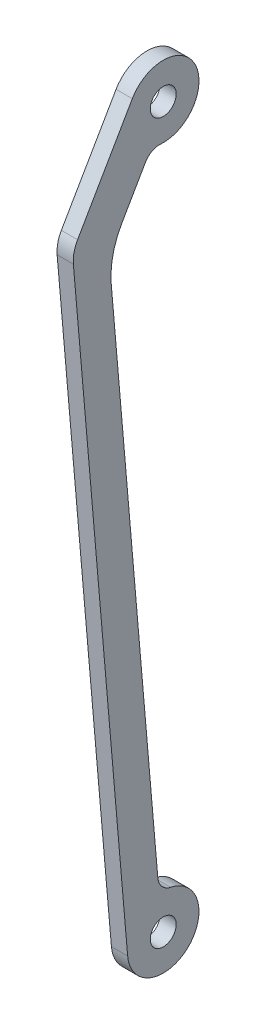
SolidWorks part; units mm, degrees
ref_plane "Front Plane" through (0, 0, 0) normal (0, 0, 1) x (1, 0, 0)
ref_plane "Top Plane" through (0, 0, 0) normal (0, 1, 0) x (1, 0, 0)
ref_plane "Right Plane" through (0, 0, 0) normal (1, 0, 0) x (0, 0, -1)
sketch "Sketch1" plane through (0, 0, 0) normal (0, 1, 0) x (1, 0, 0)
  line L1 (-5.5, -9.5263) -> (23.6733, -26.3695)
  line L2 (40.742, -16.0057) -> (206.1791, -1.6657)
  line L3 (26.0831, -12.7497) -> (13.4599, -5.4617)
  line L6 (29.5368, -27.6719) -> (222.3499, -10.9589)
  circle A0 centre (0, 0) radius 4
  arc A1 (10.9725, -0.778) -> (-5.5, -9.5263) centre (0, 0) ccw
  circle A2 centre (221.4, 0) radius 4
  arc A3 (222.3499, -10.9589) -> (210.6388, 2.2795) centre (221.4, 0) ccw
  arc A4 (10.9725, -0.778) -> (13.4599, -5.4617) centre (15.9599, -1.1316) ccw
  arc A5 (26.0831, -12.7497) -> (40.742, -16.0057) centre (38.5831, 8.9009) ccw
  arc A6 (206.1791, -1.6657) -> (210.6388, 2.2795) centre (205.7473, 3.3156) ccw
  arc A8 (23.6733, -26.3695) -> (29.5368, -27.6719) centre (28.6733, -17.7092) ccw
  dimension "D1" = 8
  dimension "D2" = 22
  dimension "D4" = 8
  dimension "D5" = 22
  dimension "D6" = 10
  dimension "D7" = 50
  dimension "D8" = 227.8499
  dimension "D9" = 193.5361
  dimension "D10" = 33.6864
  dimension "D13" = 10
  dimension "D12" = 10.655
  dimension "D14" = 10
  dimension "D3" = 221.4
  dimension "D11" = 13
  dimension "D15" = 166.0574
  dimension "D16" = 14.576
extrude "Boss-Extrude1" add sketch "Sketch1" along normal blind 5
move or copy body "Body-Move/Copy1" bodies to move or copy 101 copy no rotation origin (110.7, 2.5, 0) rotation axis (0, 0, -1) rotation angle 90
